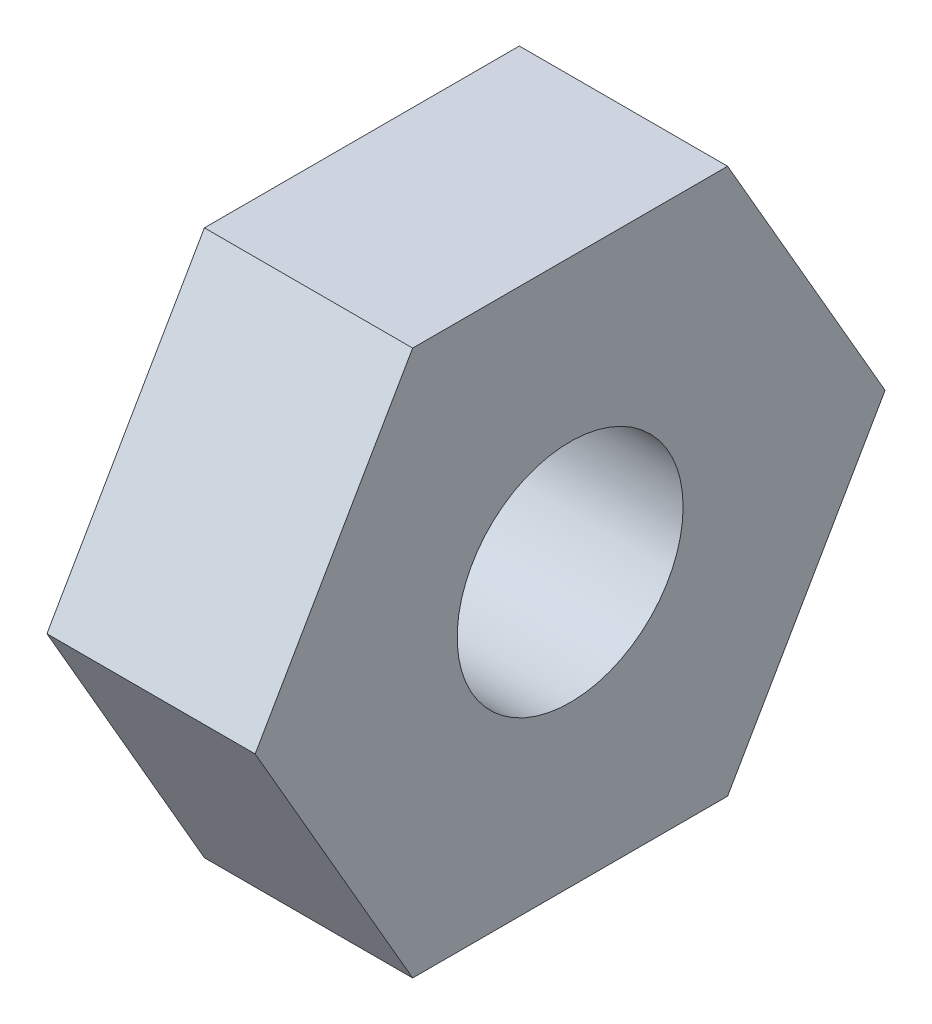
SolidWorks part; units mm, degrees
material "ABS"
ref_plane "Front Plane" through (0, 0, 0) normal (0, 0, 1) x (1, 0, 0)
ref_plane "Top Plane" through (0, 0, 0) normal (0, 1, 0) x (1, 0, 0)
ref_plane "Right Plane" through (0, 0, 0) normal (1, 0, 0) x (0, 0, -1)
sketch "Sketch1" plane through (0, 0, 0) normal (1, 0, 0) x (0, 0, -1)
  line L1 (3.4569, -5.9875) -> (6.9138, 0)
  line L2 (6.9138, 0) -> (3.4569, 5.9875)
  line L3 (3.4569, 5.9875) -> (-3.4569, 5.9875)
  line L4 (-3.4569, 5.9875) -> (-6.9138, 0)
  line L5 (-6.9138, 0) -> (-3.4569, -5.9875)
  line L6 (-3.4569, -5.9875) -> (3.4569, -5.9875)
  circle A0 centre (0, 0) radius 5.9875 construction
  circle A1 centre (0, 0) radius 2.48
  dimension "D1" = 4.96
  dimension "D2" = 11.975
extrude "Boss-Extrude1" add sketch "Sketch1" along normal blind 4.572
sketch "Sketch2" plane through (0, 0, 0) normal (1, 0, 0) x (0, 0, -1)
  circle A0 centre (0, 0) radius 3.81
  circle A1 centre (0, 0) radius 2.48
  dimension "D1" = 7.62
extrude "Boss-Extrude2" add sketch "Sketch2" against normal blind 1.016
